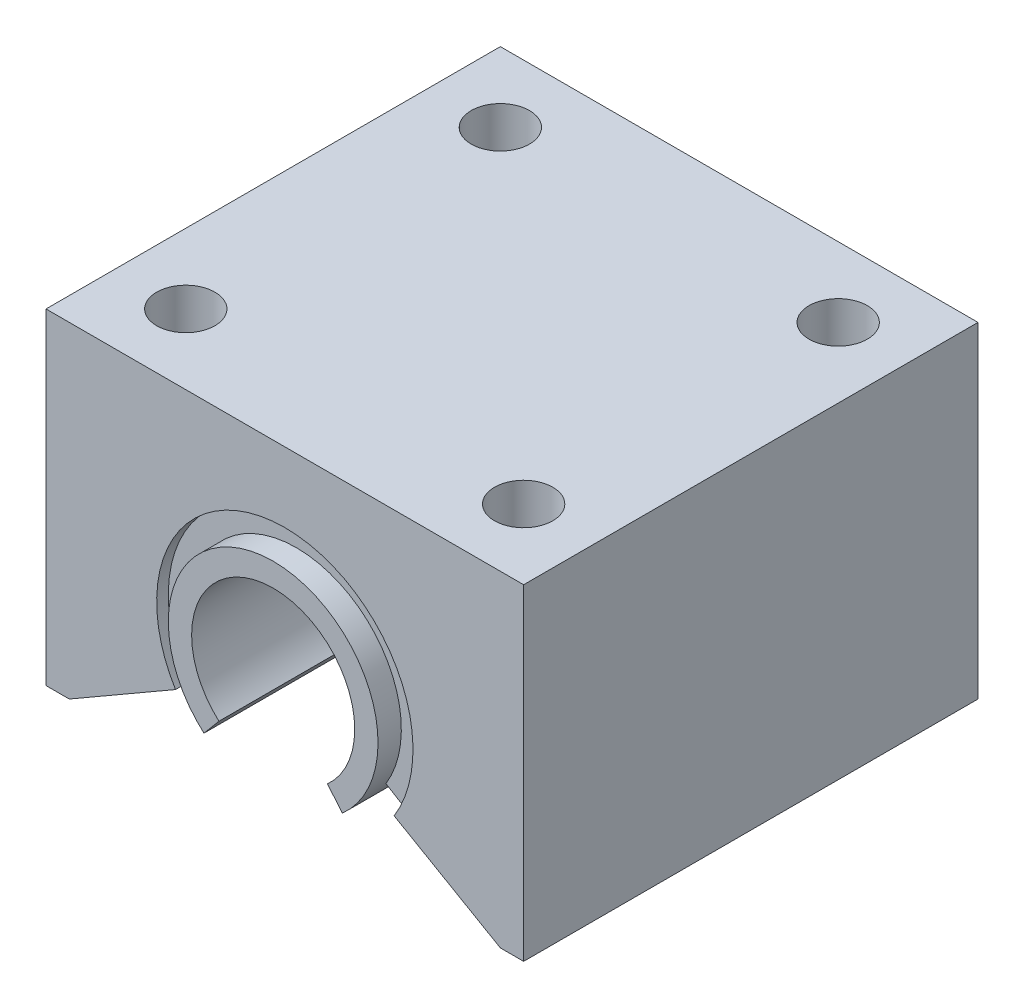
SolidWorks part; units mm, degrees
ref_plane "Front Plane" through (0, 0, 0) normal (0, 0, 1) x (1, 0, 0)
ref_plane "Top Plane" through (0, 0, 0) normal (0, 1, 0) x (1, 0, 0)
ref_plane "Right Plane" through (0, 0, 0) normal (1, 0, 0) x (0, 0, -1)
sketch "Sketch1" plane through (0, 0, 0) normal (0, 0, 1) x (1, 0, 0)
  line L1 (-20.5, 14) -> (20.5, 14)
  line L2 (-20.5, 14) -> (-20.5, -14)
  line L3 (-20.5, -14) -> (-18.5, -14)
  line L4 (20.5, 14) -> (20.5, -14)
  line L5 (-20.5, 14) -> (20.5, -14) construction
  line L6 (-20.5, -14) -> (20.5, 14) construction
  line L7 (0, 0) -> (0, -20.1822) construction
  line L9 (-18.5, -14) -> (-9.3851, -8.7375)
  line L10 (18.5, -14) -> (9.3851, -8.7375)
  line L11 (18.5, -14) -> (20.5, -14)
  arc A0 (9.3851, -8.7375) -> (-9.3851, -8.7375) centre (0, -3) ccw
  point P0 (0, 0)
  dimension "D3" = 11
  dimension "D1" = 41
  dimension "D2" = 28
  dimension "D4" = 2
extrude "Boss-Extrude1" add sketch "Sketch1" along normal blind 39
sketch "Sketch2" plane through (0, 0, 0) normal (0, 0, 1) x (1, 0, 0)
  line L0 (-9.3851, -8.7375) -> (-7.6787, -7.6943)
  line L2 (9.3851, -8.7375) -> (7.6787, -7.6943)
  arc A0 (9.3851, -8.7375) -> (-9.3851, -8.7375) centre (0, -3) ccw
  arc A1 (7.6787, -7.6943) -> (-7.6787, -7.6943) centre (0, -3) ccw
  circle A3 centre (0, -3) radius 9 construction
  circle A4 centre (0, -3) radius 11 construction
  point P4 (10.5194, 0.2161)
  point P11 (9, -3)
  dimension "D1" = 2
extrude "Boss-Extrude3" add sketch "Sketch2" along normal blind 37 from offset 1 separate body
sketch "Sketch3" plane through (0, 0, 0) normal (0, 0, 1) x (1, 0, 0)
  line L0 (0, -3) -> (0, -16.4583) construction
  line L1 (-5.9419, -9.7597) -> (-4.6559, -8.2271)
  line L2 (5.9419, -9.7597) -> (4.6559, -8.2271)
  arc A0 (5.9419, -9.7597) -> (-5.9419, -9.7597) centre (0, -3) ccw
  arc A1 (4.6559, -8.2271) -> (-4.6559, -8.2271) centre (0, -3) ccw
  circle A3 centre (0, -3) radius 7 construction
  circle A4 centre (0, -3) radius 9 construction
  point P5 (8.6067, -0.3687)
  point P6 (7, -3)
  dimension "D1" = 2
extrude "Boss-Extrude4" add sketch "Sketch3" along normal blind 41 from offset 1 offset against normal yes
sketch "Sketch4" plane through (0, 14, 0) normal (0, 1, 0) x (1, 0, 0)
  line L0 (20.5, -39) -> (-20.5, -39) construction
  line L5 (20.5, -39) -> (20.5, 0) construction
  circle A0 centre (-14.5, -6) radius 2.5
  circle A1 centre (14.5, -6) radius 2.5
  circle A2 centre (14.5, -33) radius 2.5
  circle A3 centre (-14.5, -33) radius 2.5
  dimension "D1" = 5
  dimension "D2" = 6
  dimension "D3" = 6
  dimension "D6" = 6
  dimension "D7" = 6
  dimension "D8" = 27
  dimension "D9" = 29
  dimension "D4" = 2
  dimension "D5" = 2
extrude "Cut-Extrude1" cut sketch "Sketch4" against normal blind 10
hole_wizard "Tap Drill for M5x0.8 Tap1" positions "Sketch7" profile "Sketch8" hole size "M5x0.8" standard "ANSI Metric"
sketch "Sketch7" plane through (0, 4, 0) normal (0, 1, 0) x (1, 0, 0)
  point P0 (-14.5, -33)
  point P3 (-14.5, -6)
  point P6 (14.5, -6)
  point P9 (14.5, -33)
sketch "Sketch8" plane through (-14.5, 4, 33) normal (1, 0, 0) x (0, 0, 1)
  line L0 (0, 0) -> (0, 1.3118)
  line L1 (0, 1.3118) -> (2.1, 0.05)
  line L2 (2.1, 0.05) -> (2.1, 0.025)
  line L3 (2.1, 0.025) -> (2.125, 0)
  line L5 (2.125, 0) -> (0, 0)
  line L6 (-2.1, 0.025) -> (-2.125, 0) construction
  line L10 (0, 1.3118) -> (-2.1, 0.05) construction
  line L11 (0, -6.35) -> (0, 107.95) construction
  dimension "Hole Dia." = 4.2
  dimension "Hole Depth" = 0.05
  dimension "Near C'Sink Dia." = 4.25
  dimension "Near C'Sink Angle" = 90
  dimension "Drill Angle" = 118
